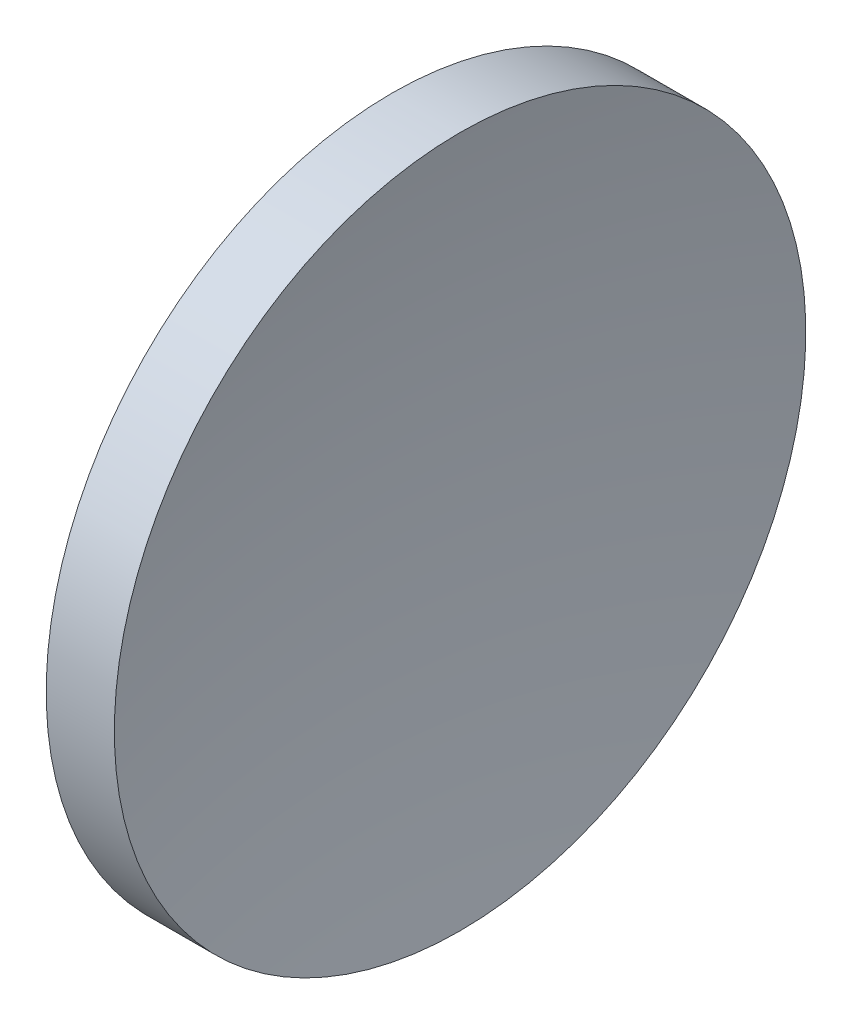
SolidWorks part; units mm, degrees
ref_plane "前视基准面" through (0, 0, 0) normal (0, 0, 1) x (1, 0, 0)
ref_plane "上视基准面" through (0, 0, 0) normal (0, 1, 0) x (1, 0, 0)
ref_plane "右视基准面" through (0, 0, 0) normal (1, 0, 0) x (0, 0, -1)
sketch "草图1" plane through (0, 0, 0) normal (0, 0, 1) x (1, 0, 0)
  line L0 (115.9445, 65.2168) -> (135.9482, 65.2168) construction
  line L1 (128.6409, 77.7168) -> (126.1767, 77.7168)
  line L2 (127.4122, 65.2168) -> (122.6122, 65.2168)
  arc A0 (126.1767, 77.7168) -> (122.6122, 65.2168) centre (146.3122, 65.2168) ccw
  arc A1 (128.6409, 77.7168) -> (127.4122, 65.2168) centre (191.6122, 65.2168) ccw
revolve "旋转1" add sketch "草图1" angle 360 about L0
